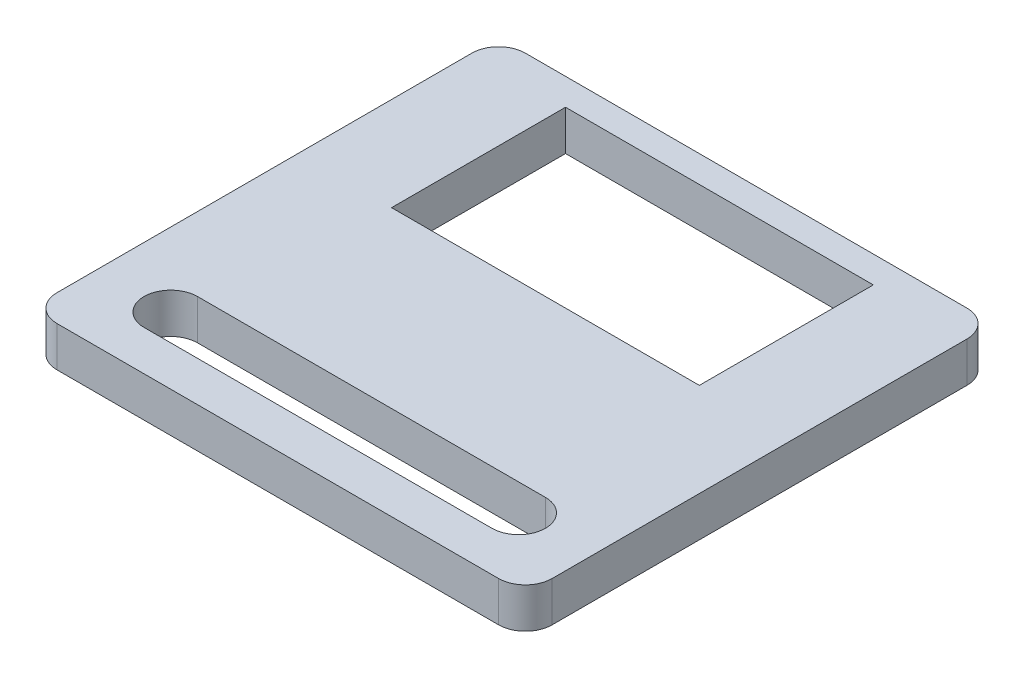
SolidWorks part; units mm, degrees
ref_plane "Front Plane" through (0, 0, 0) normal (0, 0, 1) x (1, 0, 0)
ref_plane "Top Plane" through (0, 0, 0) normal (0, 1, 0) x (1, 0, 0)
ref_plane "Right Plane" through (0, 0, 0) normal (1, 0, 0) x (0, 0, -1)
sketch "Sketch1" plane through (0, 0, 0) normal (0, 1, 0) x (1, 0, 0)
  line L0 (0, 0) -> (0, 9) construction
  line L1 (-18.5, -17.5) -> (18.5, -17.5)
  line L2 (-18.5, -17.5) -> (-18.5, 17.5)
  line L3 (-18.5, 17.5) -> (18.5, 17.5)
  line L4 (18.5, -17.5) -> (18.5, 17.5)
  line L5 (-18.5, -17.5) -> (18.5, 17.5) construction
  line L6 (-18.5, 17.5) -> (18.5, -17.5) construction
  line L7 (-11.5, 15.5) -> (11.5, 15.5)
  line L8 (-11.5, 15.5) -> (-11.5, 2.5)
  line L9 (-11.5, 2.5) -> (11.5, 2.5)
  line L10 (11.5, 15.5) -> (11.5, 2.5)
  line L11 (-11.5, 15.5) -> (11.5, 2.5) construction
  line L12 (-11.5, 2.5) -> (11.5, 15.5) construction
  line L13 (0, -12.5) -> (0, -10.5) construction
  line L14 (-13, -10.5) -> (13, -10.5)
  line L16 (-13, -14.5) -> (13, -14.5)
  line L18 (-15, -10.5) -> (15, -14.5) construction
  line L19 (-15, -14.5) -> (15, -10.5) construction
  arc A1 (-13, -10.5) -> (-13, -14.5) centre (-13, -12.5) ccw
  arc A2 (13, -10.5) -> (13, -14.5) centre (13, -12.5) cw
  point P0 (0, 0)
  point P5 (0, 9)
  point P13 (0, -12.5)
  dimension "D9" = 2
  dimension "D1" = 35
  dimension "D2" = 37
  dimension "D3" = 7
  dimension "D4" = 13
  dimension "D5" = 2
  dimension "D6" = 4
  dimension "D7" = 3
extrude "Boss-Extrude1" add sketch "Sketch1" along normal blind 3
fillet "Fillet1" radius 2 4 edges at (18.5, 1.5, -17.5) (18.5, 1.5, 17.5) (-18.5, 1.5, 17.5) (-18.5, 1.5, -17.5)
